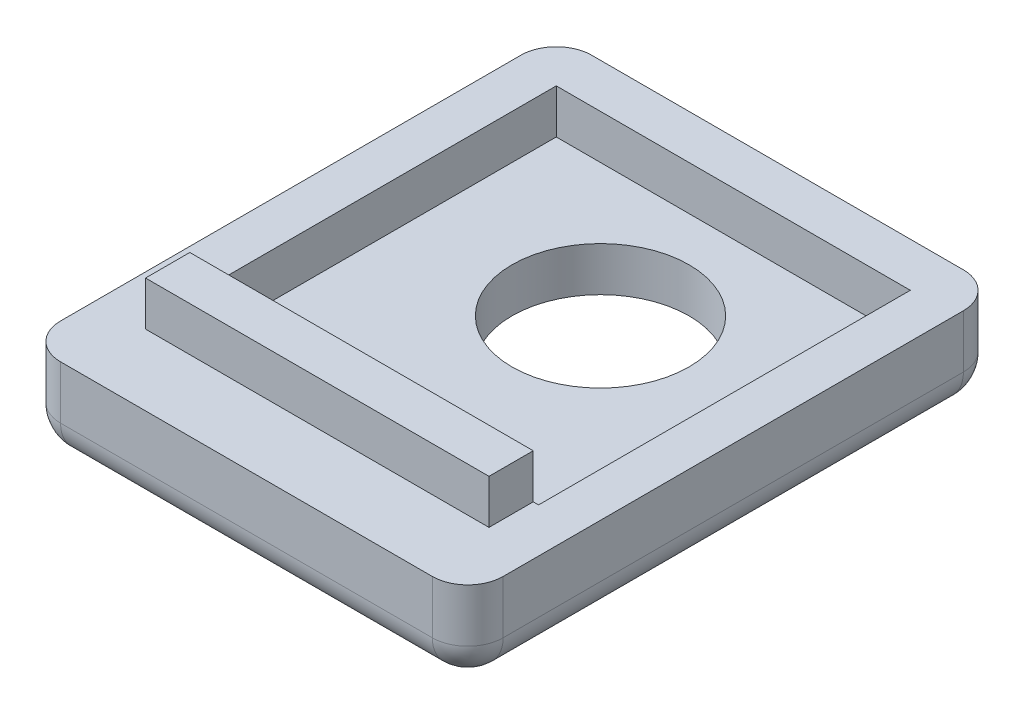
SolidWorks part; units mm, degrees
ref_plane "Front Plane" through (0, 0, 0) normal (0, 0, 1) x (1, 0, 0)
ref_plane "Top Plane" through (0, 0, 0) normal (0, 1, 0) x (1, 0, 0)
ref_plane "Right Plane" through (0, 0, 0) normal (1, 0, 0) x (0, 0, -1)
sketch "Sketch1" plane through (0, 0, 0) normal (0, 1, 0) x (1, 0, 0)
  line L1 (-12.5, 15) -> (12.5, 15)
  line L2 (-12.5, 15) -> (-12.5, -15)
  line L3 (-12.5, -15) -> (12.5, -15)
  line L4 (12.5, 15) -> (12.5, -15)
  line L5 (-12.5, 15) -> (12.5, -15) construction
  line L6 (-12.5, -15) -> (12.5, 15) construction
  point P0 (0, 0)
  dimension "D1" = 30
  dimension "D2" = 25
extrude "Boss-Extrude1" add sketch "Sketch1" along normal blind 2.5
sketch "Sketch3" plane through (0, 2.5, 0) normal (0, 1, 0) x (1, 0, 0)
  line L0 (0, 0) -> (0, -15) construction
  line L1 (-12.5, 15) -> (12.5, 15)
  line L2 (-12.5, 15) -> (-12.5, -15)
  line L3 (-12.5, -15) -> (12.5, -15)
  line L4 (12.5, 15) -> (12.5, -15)
  line L5 (-10, 12.5) -> (10, 12.5)
  line L6 (-10, 12.5) -> (-10, -8.5)
  line L7 (-10, -8.5) -> (10, -8.5)
  line L8 (10, 12.5) -> (10, -8.5)
  dimension "D1" = 6.5
  dimension "D2" = 2.5
  dimension "D3" = 2.5
extrude "Boss-Extrude2" add sketch "Sketch3" along normal blind 2.5
sketch "Sketch5" plane through (0, 2.5, 0) normal (0, 1, 0) x (1, 0, 0)
  line L0 (0, 0) -> (0, 5) construction
  circle A1 centre (0, 5) radius 5
  dimension "D1" = 10
  dimension "D2" = 5
extrude "Cut-Extrude1" cut sketch "Sketch5" against normal blind 2.5
fillet "Fillet2" radius 2 8 edges at (-12.5, 0, 0) (-12.5, 2.5, -15) (12.5, 0, 0) (12.5, 2.5, -15) (0, 0, 15) (12.5, 2.5, 15) (-12.5, 2.5, 15) (0, 0, -15)
sketch "Sketch6" plane through (0, 5, 0) normal (0, 1, 0) x (1, 0, 0)
  line L0 (-10, -8.5) -> (10, -8.5) construction
  line L1 (-9.7, -8.5) -> (9.7, -8.5)
  line L2 (-9.7, -8.5) -> (-9.7, -11)
  line L3 (-9.7, -11) -> (9.7, -11)
  line L4 (9.7, -8.5) -> (9.7, -11)
  line L5 (0, 0) -> (0, -15) construction
  line L6 (-10.5, -15) -> (10.5, -15) construction
  line L7 (10, -8.5) -> (10, 12.5) construction
  dimension "D1" = 2.5
  dimension "D2" = 0.3
extrude "Boss-Extrude4" add sketch "Sketch6" along normal blind 2.5
